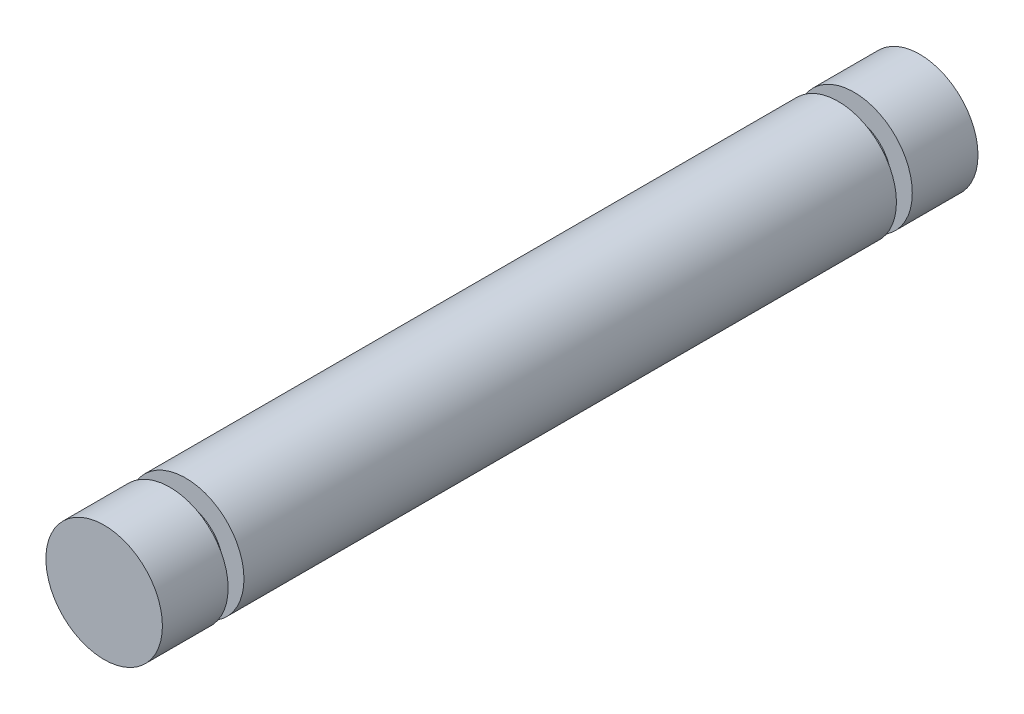
SolidWorks part; units mm, degrees
ref_plane "Front Plane" through (0, 0, 0) normal (0, 0, 1) x (1, 0, 0)
ref_plane "Top Plane" through (0, 0, 0) normal (0, 1, 0) x (1, 0, 0)
ref_plane "Right Plane" through (0, 0, 0) normal (1, 0, 0) x (0, 0, -1)
sketch "Sketch1" plane through (0, 0, 0) normal (0, 0, 1) x (1, 0, 0)
  circle A0 centre (0, 0) radius 2.5
  dimension "D1" = 5
extrude "Boss-Extrude1" add sketch "Sketch1" along normal blind 35
sketch "Sketch2" plane through (0, 0, 0) normal (1, 0, 0) x (0, 0, -1)
  line L0 (-35, 2.5) -> (-32.18, 2.5) construction
  line L1 (0, 2.5) -> (-35, 2.5) construction
  line L2 (-32.18, 2.5) -> (-32.18, 1.6)
  line L3 (-32.18, 1.6) -> (-31.5, 1.6)
  line L4 (-31.5, 1.6) -> (-31.5, 2.5)
  line L5 (-31.5, 2.5) -> (-32.18, 2.5)
  line L6 (-35, -2.5) -> (-32.18, -2.5) construction
  line L7 (-35, -2.5) -> (0, -2.5) construction
  line L8 (-32.18, -2.5) -> (-32.18, -1.6) construction
  line L9 (-32.18, -1.6) -> (-31.5, -1.6) construction
  line L10 (-31.5, -1.6) -> (-31.5, -2.5) construction
  line L11 (-31.5, -2.5) -> (-32.18, -2.5) construction
  line L12 (-35, 0) -> (0, 0) construction
  line L13 (-35, 2.5) -> (-35, -2.5) construction
  line L14 (-17.5, 2.5) -> (-17.5, -2.5) construction
  line L15 (0, 2.5) -> (-2.82, 2.5) construction
  line L16 (-3.5, 2.5) -> (-2.82, 2.5)
  line L17 (-3.5, 1.6) -> (-3.5, 2.5)
  line L18 (-2.82, 1.6) -> (-3.5, 1.6)
  line L19 (-2.82, 2.5) -> (-2.82, 1.6)
  dimension "D1" = 0.68
  dimension "D2" = 3.2
  dimension "D3" = 3.5
revolve "Cut-Revolve1" cut sketch "Sketch2" angle 360 about L12
